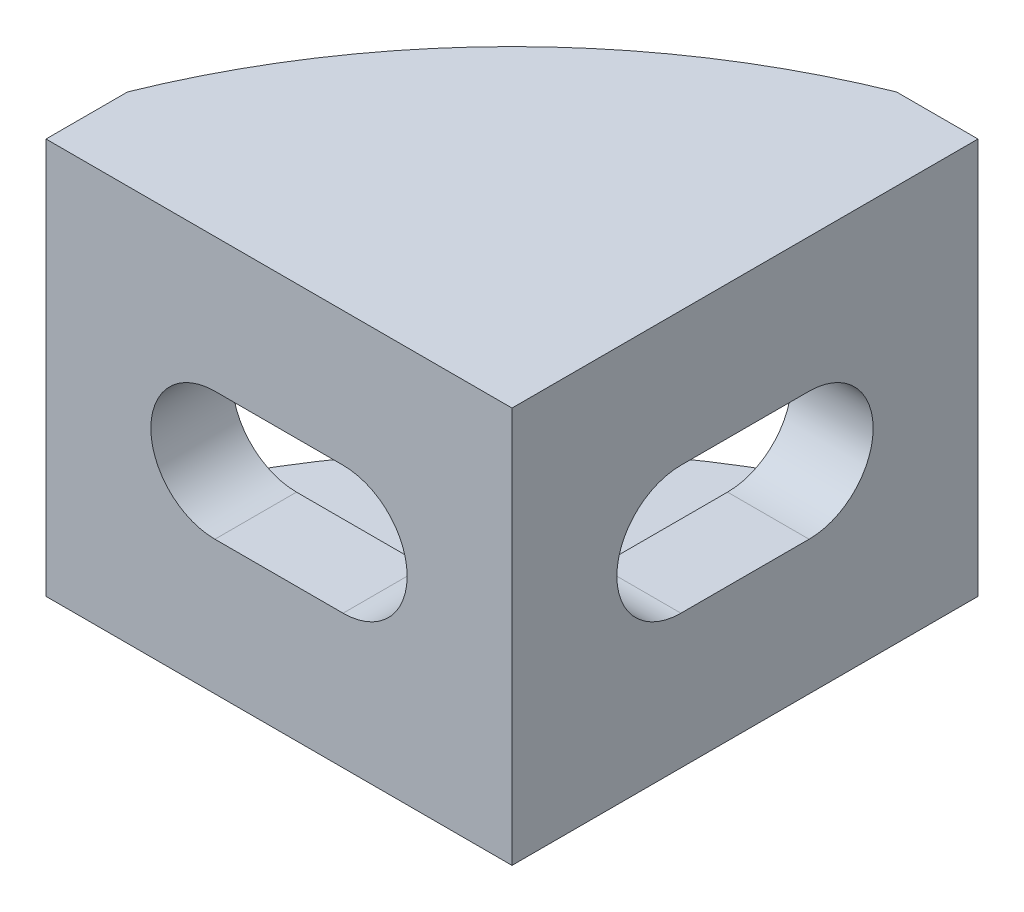
SolidWorks part; units mm, degrees
ref_plane "Front Plane" through (0, 0, 0) normal (0, 0, 1) x (1, 0, 0)
ref_plane "Top Plane" through (0, 0, 0) normal (0, 1, 0) x (1, 0, 0)
ref_plane "Right Plane" through (0, 0, 0) normal (1, 0, 0) x (0, 0, -1)
sketch "Sketch1" plane through (0, 0, 0) normal (0, 1, 0) x (1, 0, 0)
  line L0 (0, 20) -> (0, 0)
  line L1 (0, 0) -> (-20, 0)
  line L2 (-20, 0) -> (-20, 3.5)
  line L3 (0, 20) -> (-3.5, 20)
  arc A0 (-3.5, 20) -> (-20, 3.5) centre (7.6037, -7.6037) ccw
  point P7 (-13.435, 13.435)
  dimension "D1" = 20
  dimension "D2" = 3.5
  dimension "D3" = 19
extrude "Boss-Extrude1" add sketch "Sketch1" along normal mid plane 17
sketch "Sketch2" plane through (-20, 0, 0) normal (-1, 0, 0) x (0, 0, 1)
  line L0 (-3.5, 8.5) -> (-3.5, -8.5) construction
  line L1 (-3.5, -6.5) -> (-20, -6.5)
  line L2 (-3.5, -6.5) -> (-3.5, 6.5)
  line L3 (-3.5, 6.5) -> (-20, 6.5)
  line L4 (-20, -6.5) -> (-20, 6.5)
  line L5 (-20, 8.5) -> (-20, -8.5) construction
  line L6 (-3.5, 8.5) -> (-20, 8.5) construction
  point P8 (-3.5, 0)
  dimension "D1" = 2
extrude "Cut-Extrude1" cut sketch "Sketch2" against normal up to vertex (16.5 mm away)
sketch "Sketch4" plane through (0, 0, 0) normal (0, 0, 1) x (1, 0, 0)
  line L0 (-7.25, 2.75) -> (-12.75, 2.75)
  line L1 (-12.75, -2.75) -> (-7.25, -2.75)
  line L3 (-20, 8.5) -> (-20, -8.5) construction
  arc A0 (-12.75, 2.75) -> (-12.75, -2.75) centre (-12.75, 0) ccw
  arc A1 (-7.25, -2.75) -> (-7.25, 2.75) centre (-7.25, 0) ccw
  point P6 (-4.5, 0)
  point P8 (-15.5, 0)
  point P9 (-6.0286, 0)
  dimension "D1" = 5.5
  dimension "D2" = 11
  dimension "D3" = 4.5
extrude "Cut-Extrude2" cut sketch "Sketch4" against normal up to surface (3.5 mm away) up to face at (-11.75, 0, -3.5)
sketch "Sketch5" plane through (0, 0, 0) normal (1, 0, 0) x (0, 0, -1)
  line L0 (7.25, 2.75) -> (12.75, 2.75)
  line L1 (12.75, -2.75) -> (7.25, -2.75)
  line L2 (20, 8.5) -> (20, -8.5) construction
  arc A0 (12.75, 2.75) -> (12.75, -2.75) centre (12.75, 0) cw
  arc A1 (7.25, -2.75) -> (7.25, 2.75) centre (7.25, 0) cw
  point P5 (15.5, 0)
  point P7 (4.5, 0)
  point P10 (0, 0)
  dimension "D1" = 11
  dimension "D2" = 5.5
  dimension "D3" = 4.5
extrude "Cut-Extrude3" cut sketch "Sketch5" against normal up to surface (3.5 mm away) up to face at (-3.5, 0, -11.75)
